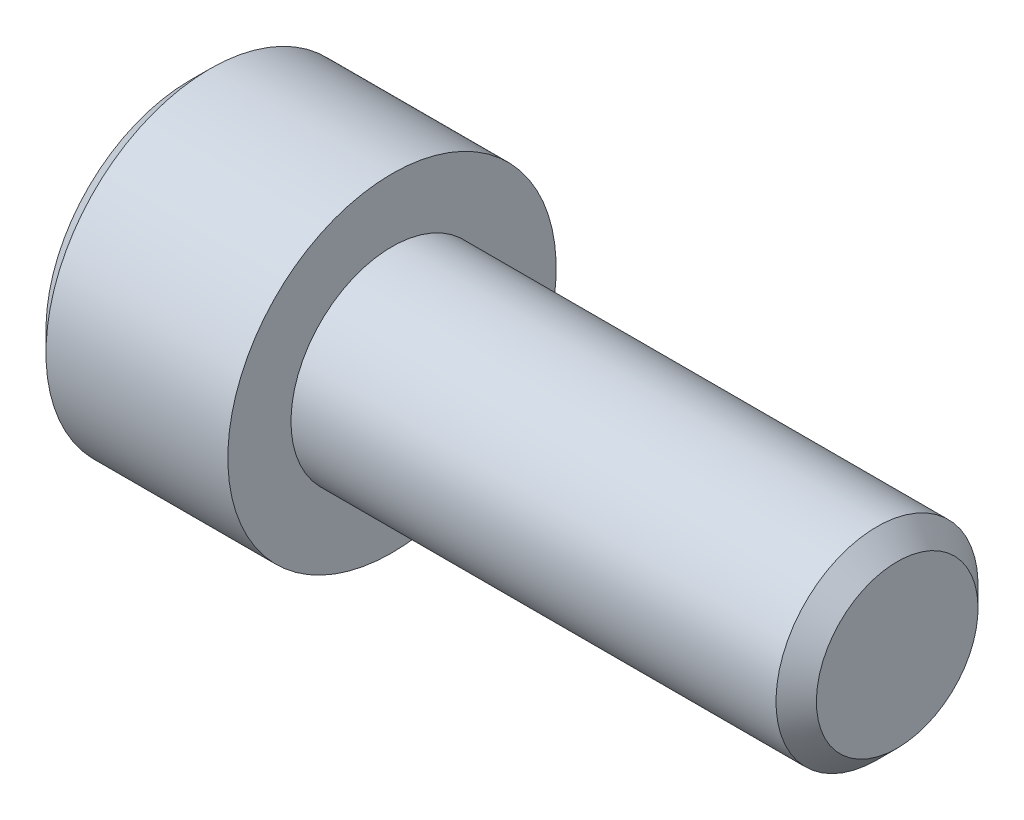
SolidWorks part; units mm, degrees
ref_plane "Front" through (0, 0, 0) normal (0, 0, 1) x (1, 0, 0)
ref_plane "Top" through (0, 0, 0) normal (0, 1, 0) x (1, 0, 0)
ref_plane "Right" through (0, 0, 0) normal (1, 0, 0) x (0, 0, -1)
ref_plane "Plane1" through (0, 0, 0) normal (0, 0, 1) x (1, 0, 0)
sketch "Sketch1" plane through (0, 0, 0) normal (0, 0, 1) x (1, 0, 0)
  line L0 (-8, 0) -> (-8, 6.5)
  line L1 (-8, 6.5) -> (0, 6.5)
  line L2 (0, 6.5) -> (0, 4)
  line L3 (0, 4) -> (20, 4)
  line L5 (20, 4) -> (20, 0)
  line L6 (20, 0) -> (-8, 0)
  line L7 (20, 0) -> (-8, 0) construction
  dimension "D1" = 20
  dimension "D2" = 8
  dimension "D3" = 4
  dimension "D4" = 6.5
revolve "Revolve1" add sketch "Sketch1" angle 360 about L7
ref_plane "Plane2" through (0, 0, 0) normal (0, 0, 1) x (1, 0, 0)
chamfer "Chamfer1" distance 0.8 angle 45 2 edges at (20, -4, 0) (-8, -6.5, 0)
sketch "Sketch2" plane through (0, 0, 0) normal (0, 0, 1) x (1, 0, 0)
  line L0 (-8, 0) -> (-8, 3)
  line L1 (-8, 3) -> (-4, 3)
  line L2 (-4, 3) -> (-3.1962, 0)
  line L3 (-3.1962, 0) -> (-8, 0)
  line L4 (-3.1962, 0) -> (-8, 0) construction
revolve "Cut-Revolve1" cut sketch "Sketch2" angle 360 about L4
ref_plane "Plane3" through (-8, 0, 0) normal (1, 0, 0) x (0, 0, -1)
sketch "Sketch3" plane through (-8, 0, 0) normal (1, 0, 0) x (0, 0, -1)
  line L0 (-3, 1.7321) -> (-3, -1.7321)
  line L1 (-3, -1.7321) -> (0, -3.4641)
  line L2 (0, -3.4641) -> (3, -1.7321)
  line L3 (3, -1.7321) -> (3, 1.7321)
  line L4 (3, 1.7321) -> (0, 3.4641)
  line L5 (0, 3.4641) -> (-3, 1.7321)
extrude "Cut-Extrude1" cut sketch "Sketch3" along normal blind 4
